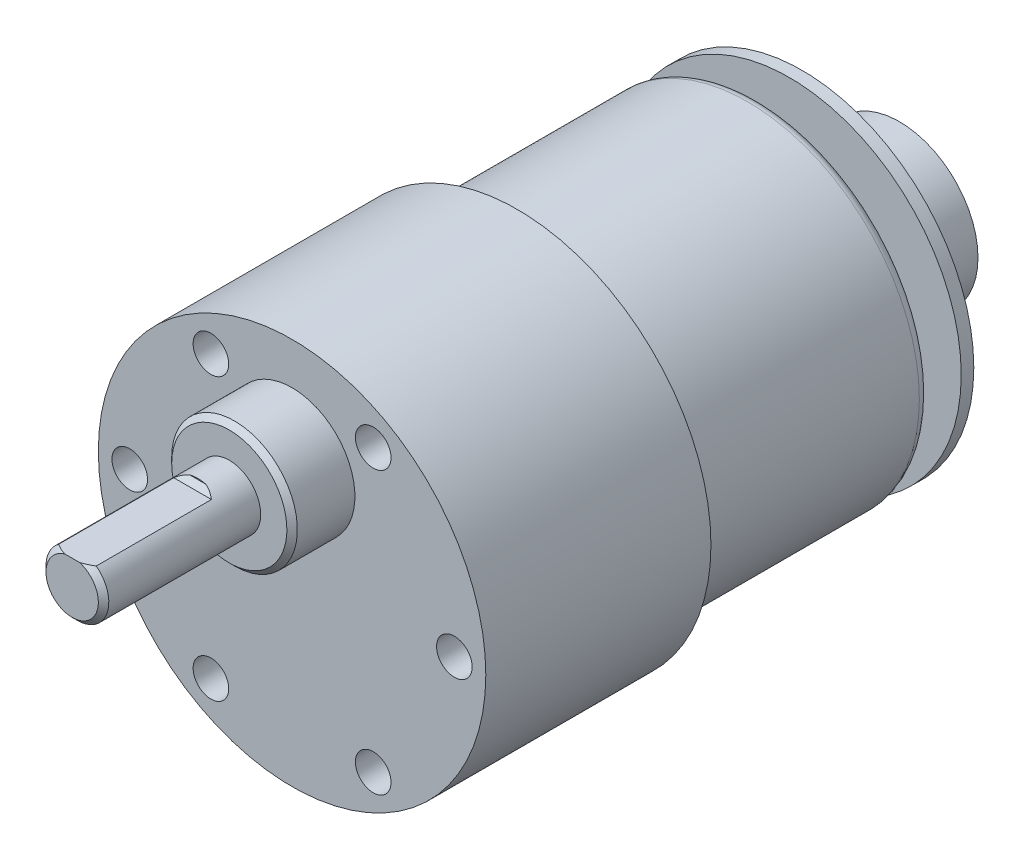
SolidWorks part; units mm, degrees
material "Acier allié"
ref_plane "Plan de face" through (0, 0, 0) normal (0, 0, 1) x (1, 0, 0)
ref_plane "Plan de dessus" through (0, 0, 0) normal (0, 1, 0) x (1, 0, 0)
ref_plane "Plan de droite" through (0, 0, 0) normal (1, 0, 0) x (0, 0, -1)
sketch "Esquisse1" plane through (0, 0, 0) normal (1, 0, 0) x (0, 0, -1)
  line L0 (0, 0) -> (0, 16.4)
  line L1 (0, 16.4) -> (-23, 16.4)
  line L2 (-23, 16.4) -> (-23, 18.5)
  line L3 (-23, 18.5) -> (-44.5, 18.5)
  line L4 (-44.5, 18.5) -> (-44.5, 0)
  line L5 (-44.5, 0) -> (0, 0) construction
  line L6 (0, 0) -> (-44.5, 0)
  dimension "D1" = 23
  dimension "D2" = 16.4
  dimension "D3" = 18.5
  dimension "D4" = 21.5
revolve "Révolution1" add sketch "Esquisse1" angle 360 about L5
sketch "Esquisse3" plane through (0, 0, 0) normal (1, 0, 0) x (0, 0, -1)
  line L0 (-44.5, 14.5) -> (-50.4953, 14.5)
  line L1 (-44.5, 18.5) -> (-44.5, -18.5) construction
  line L2 (-50.4953, 14.5) -> (-50.4953, 8.5)
  line L3 (-50.4953, 8.5) -> (-44.5, 8.5)
  line L4 (-44.5, 8.5) -> (-44.5, 14.5)
  line L5 (-23, 18.5) -> (-44.5, 18.5) construction
  dimension "D1" = 5.9953
  dimension "D2" = 6
  dimension "D3" = 4
revolve "Révolution2" add sketch "Esquisse3" angle 360 about L3
sketch "Esquisse4" plane through (0, 0, 0) normal (1, 0, 0) x (0, 0, -1)
  line L0 (-50.4953, 8.5) -> (-65.5, 8.5)
  line L1 (-50.4953, 14.5) -> (-50.4953, 2.5) construction
  line L2 (-65.5, 8.5) -> (-65.5, 11.5)
  line L3 (-65.5, 11.5) -> (-50.4953, 11.5)
  line L4 (-50.4953, 11.5) -> (-50.4953, 8.5)
  line L5 (-44.5, 18.5) -> (-44.5, -18.5) construction
  dimension "D1" = 21
  dimension "D2" = 3
revolve "Révolution3" add sketch "Esquisse4" angle 360 about L0
sketch "Esquisse5" plane through (0, 0, 65.5) normal (0, 0, 1) x (1, 0, 0)
  line L1 (-2.5, 11.9) -> (2.5, 11.9)
  line L2 (-2.5, 11.9) -> (-2.5, 10.9)
  line L3 (-2.5, 10.9) -> (2.5, 10.9)
  line L4 (2.5, 11.9) -> (2.5, 10.9)
  circle A0 centre (0, 8.5) radius 3 construction
  dimension "D1" = 2.4
  dimension "D2" = 5
  dimension "D3" = 2.5
  dimension "D4" = 1
extrude "Enlèv. mat.-Extru.1" cut sketch "Esquisse5" against normal blind 12
chamfer "Chanfrein1" distance 0.5 angle 45 2 edges at (0, 5.5, 65.5) (0, 10.9, 53.5)
sketch "Esquisse6" plane through (0, 0, 0) normal (1, 0, 0) x (0, 0, -1)
  line L1 (0, 0) -> (3, 0)
  line L2 (0, 0) -> (0, 3)
  line L3 (0, 3) -> (3, 3)
  line L4 (3, 0) -> (3, 3)
  dimension "D1" = 3
  dimension "D2" = 3
revolve "Révolution4" add sketch "Esquisse6" angle 360 about L1
sketch "Esquisse7" plane through (0, 0, 0) normal (1, 0, 0) x (0, 0, -1)
  line L0 (3, -3) -> (3, 3) construction
  line L1 (3, 0) -> (4.2, 0)
  line L2 (3, 0) -> (3, 16.4)
  line L3 (3, 16.4) -> (4.2, 16.4)
  line L4 (4.2, 0) -> (4.2, 16.4)
  dimension "D1" = 1.2
  dimension "D2" = 16.4
revolve "Révolution5" add sketch "Esquisse7" angle 360 about L1
sketch "Esquisse8" plane through (0, 0, 0) normal (1, 0, 0) x (0, 0, -1)
  line L0 (4.2, -16.4) -> (4.2, 16.4) construction
  line L1 (4.2, 0) -> (13.5, 0)
  line L2 (4.2, 0) -> (4.2, 7.5)
  line L3 (4.2, 7.5) -> (13.5, 7.5)
  line L4 (13.5, 0) -> (13.5, 7.5)
  line L5 (-44.5, 18.5) -> (-44.5, -18.5) construction
  dimension "D1" = 7.5
  dimension "D2" = 58
revolve "Révolution6" add sketch "Esquisse8" angle 360 about L1
sketch "Esquisse9" plane through (0, 0, 0) normal (0, 0, 1) x (1, 0, 0)
  line L0 (0, 0) -> (15.5, 0) construction
  point P0 (15.5, 0)
  dimension "D1" = 15.5
hole_wizard "Dégagement M31" positions "Esquisse10" profile "Esquisse12" hole size "M3" standard "Ansi Metric"
sketch "Esquisse10" plane through (0, 0, 44.5) normal (0, 0, 1) x (1, 0, 0)
  point P0 (15.5, 0)
sketch "Esquisse12" plane through (15.5, 0, 44.5) normal (1, 0, 0) x (0, -1, 0)
  line L0 (0, 0) -> (0, 11.0215)
  line L1 (0, 11.0215) -> (1.7, 10)
  line L2 (1.7, 10) -> (1.7, 0)
  line L5 (1.7, 0) -> (0, 0)
  line L10 (0, 11.0215) -> (-1.7, 10) construction
  line L11 (0, -6.35) -> (0, 107.95) construction
  dimension "Diamètre du perçage" = 3.4
  dimension "Profondeur du perçage" = 10
  dimension "Angle de pointe" = 118
pattern_circular "Répétition circulaire1" count 6 over 360 about axis through (0, 0, 0) along (0, 0, 1) of "Dégagement M31"
fillet "Congé1" radius 1 1 edges at (16.4, 0, 0)
chamfer "Chanfrein2" distance 0.5 angle 45 1 edges at (0, 2.5, 50.4953)
